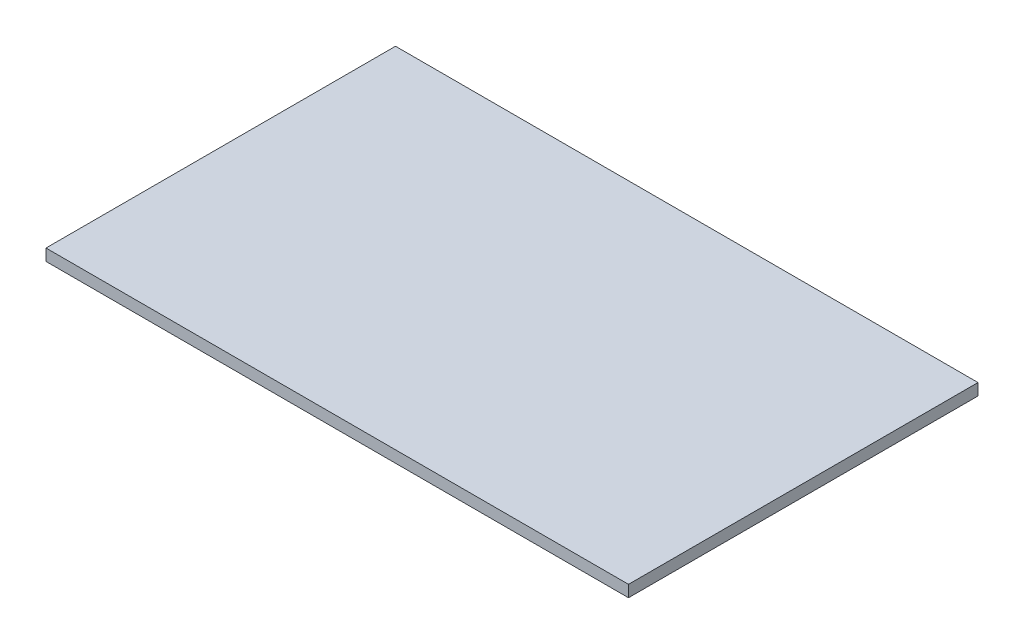
SolidWorks part; units mm, degrees
ref_plane "Front Plane" through (0, 0, 0) normal (0, 0, 1) x (1, 0, 0)
ref_plane "Top Plane" through (0, 0, 0) normal (0, 1, 0) x (1, 0, 0)
ref_plane "Right Plane" through (0, 0, 0) normal (1, 0, 0) x (0, 0, -1)
sketch "Sketch1" plane through (0, 0, 0) normal (0, 1, 0) x (1, 0, 0)
  line L1 (-55.0307, 27.9431) -> (71.9693, 27.9431)
  line L2 (-55.0307, 27.9431) -> (-55.0307, -48.2569)
  line L3 (-55.0307, -48.2569) -> (71.9693, -48.2569)
  line L4 (71.9693, 27.9431) -> (71.9693, -48.2569)
  dimension "D1" = 127
  dimension "D2" = 76.2
extrude "Boss-Extrude1" add sketch "Sketch1" along normal blind 2.54 contours L2 L3 L4 L1
